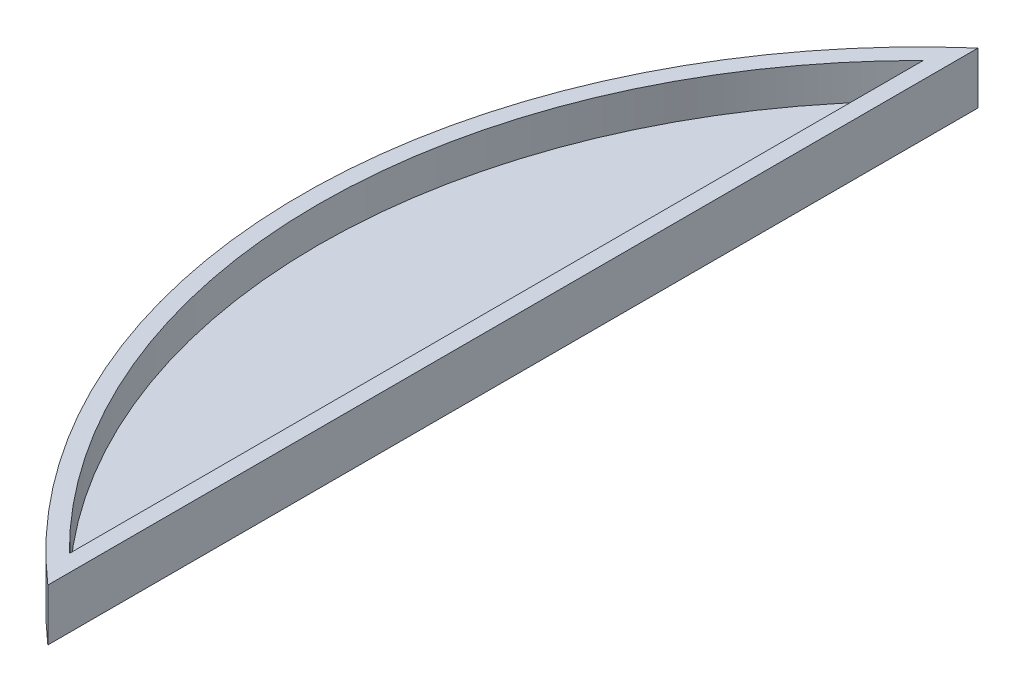
SolidWorks part; units mm, degrees
ref_plane "Front Plane" through (0, 0, 0) normal (0, 0, 1) x (1, 0, 0)
ref_plane "Top Plane" through (0, 0, 0) normal (0, 1, 0) x (1, 0, 0)
ref_plane "Right Plane" through (0, 0, 0) normal (1, 0, 0) x (0, 0, -1)
sketch "Sketch1" plane through (0, 0, 0) normal (0, 1, 0) x (1, 0, 0)
  line L0 (0, 0) -> (0, -113.792)
  circle A0 centre (49.7284, -56.896) radius 75.565
  dimension "D1" = 113.792
  dimension "D2" = 151.13
extrude "Boss-Extrude1" add sketch "Sketch1" along normal blind 6.35 contours L0 A0
shell "Shell1" thickness 2.032
